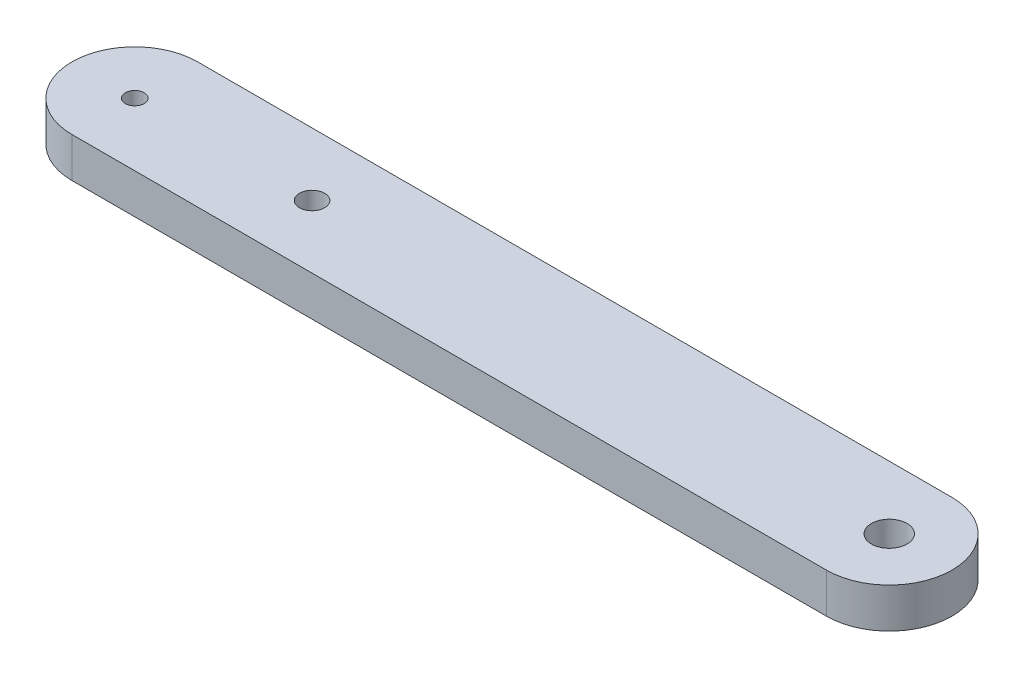
SolidWorks part; units mm, degrees
ref_plane "Front Plane" through (0, 0, 0) normal (0, 0, 1) x (1, 0, 0)
ref_plane "Top Plane" through (0, 0, 0) normal (0, 1, 0) x (1, 0, 0)
ref_plane "Right Plane" through (0, 0, 0) normal (1, 0, 0) x (0, 0, -1)
sketch "Sketch3" plane through (0, 0, 0) normal (0, 1, 0) x (1, 0, 0)
  line L0 (0, 49.0813) -> (0, -49.6192) construction
  line L1 (-30, 5) -> (30, 5)
  line L3 (-30, -5) -> (30, -5)
  line L5 (-30, 5) -> (30, -5) construction
  line L6 (-30, -5) -> (30, 5) construction
  line L7 (-69.6551, 0) -> (79.068, 0) construction
  arc A0 (30, 5) -> (30, -5) centre (30, 0) cw
  arc A1 (-30, 5) -> (-30, -5) centre (-30, 0) ccw
  circle A2 centre (30, 0) radius 1.42
  circle A3 centre (-30, 0) radius 0.75
  point P0 (0, 0)
  dimension "D2" = 10
  dimension "D3" = 2.84
  dimension "D4" = 1.5
  dimension "D1" = 60
extrude "Arm" add sketch "Sketch3" along normal blind 3.175
sketch "Sketch4" [suppressed] plane through (0, 3.175, 0) normal (0, 1, 0) x (1, 0, 0)
  circle A0 centre (0, 0) radius 1.42
  circle A2 centre (60, 0) radius 1.42 construction
extrude "Cut-Extrude1" [suppressed] cut sketch "Sketch4" against normal through all
sketch "Sketch5" plane through (0, 3.175, 0) normal (0, 1, 0) x (1, 0, 0)
  circle A0 centre (-15.9, 0) radius 1
  circle A1 centre (-30, 0) radius 0.75 construction
  dimension "D2" = 2
  dimension "D1" = 14.1
extrude "Cut-Extrude2" cut sketch "Sketch5" against normal through all
sketch "Sketch6" [suppressed] plane through (0, 0, 0) normal (0, 1, 0) x (1, 0, 0)
  circle A0 centre (0, 0) radius 5
  circle A2 centre (0, 0) radius 1.42
  dimension "D1" = 10
  dimension "D2" = 2.84
extrude "Spacer" [suppressed] add sketch "Sketch6" along normal blind 3.18
